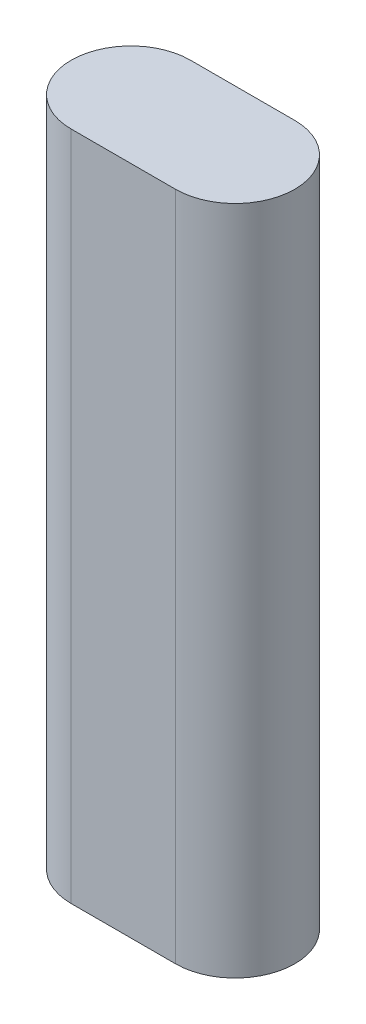
SolidWorks part; units mm, degrees
ref_plane "Front Plane" through (0, 0, 0) normal (0, 0, 1) x (1, 0, 0)
ref_plane "Top Plane" through (0, 0, 0) normal (0, 1, 0) x (1, 0, 0)
ref_plane "Right Plane" through (0, 0, 0) normal (1, 0, 0) x (0, 0, -1)
sketch "Sketch1" plane through (0, 0, 0) normal (0, 1, 0) x (1, 0, 0)
  line L0 (-10.5, 0) -> (10.5, 0) construction
  line L1 (-10.5, 12) -> (10.5, 12)
  line L2 (-10.5, -12) -> (10.5, -12)
  arc A0 (-10.5, 12) -> (-10.5, -12) centre (-10.5, 0) ccw
  arc A1 (10.5, -12) -> (10.5, 12) centre (10.5, 0) ccw
  point P2 (0, 0)
  point P8 (-22.5, 0)
  point P9 (22.5, 0)
  dimension "D1" = 24
  dimension "D2" = 45
extrude "Boss-Extrude1" add sketch "Sketch1" along normal blind 135
ref_plane "Plane1" through (0, 67.5, 0) normal (0, -1, 0) x (-1, 0, 0)
